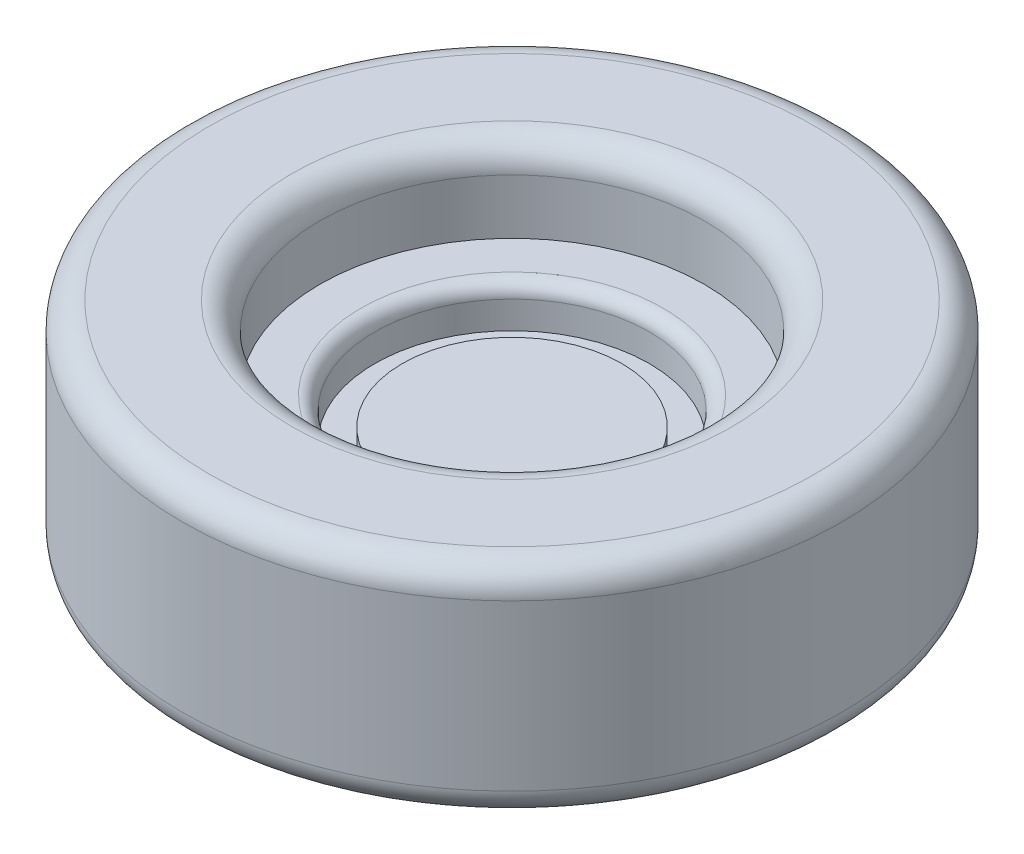
SolidWorks part; units mm, degrees
ref_plane "前视基准面" through (0, 0, 0) normal (0, 0, 1) x (1, 0, 0)
ref_plane "上视基准面" through (0, 0, 0) normal (0, 1, 0) x (1, 0, 0)
ref_plane "右视基准面" through (0, 0, 0) normal (1, 0, 0) x (0, 0, -1)
other "Configuration Table"
sketch "草图1" plane through (0, 0, 0) normal (0, 1, 0) x (1, 0, 0)
  line L1 (-20, -7.5) -> (20, -7.5)
  line L2 (-20, -7.5) -> (-20, 7.5)
  line L3 (-20, 7.5) -> (20, 7.5)
  line L4 (20, -7.5) -> (20, 7.5)
  line L5 (-20, -7.5) -> (20, 7.5) construction
  line L6 (-20, 7.5) -> (20, -7.5) construction
  point P0 (0, 0)
  dimension "D1" = 15
  dimension "D2" = 40
extrude "凸台-拉伸1" add sketch "草图1" along normal blind 1.5
sketch "草图2" plane through (0, 1.5, 0) normal (0, 1, 0) x (1, 0, 0)
  circle A0 centre (0, 0) radius 12
extrude "凸台-拉伸2" add sketch "草图2" along normal blind 8
sketch "草图3" plane through (0, 9.5, 0) normal (0, 1, 0) x (1, 0, 0)
  circle A0 centre (0, 0) radius 7
  circle A1 centre (0, 0) radius 5
extrude "切除-拉伸1" cut sketch "草图3" against normal blind 3
sketch "草图4" plane through (0, 9.5, 0) normal (0, 1, 0) x (1, 0, 0)
  circle A1 centre (0, 0) radius 5
  circle A2 centre (0, 0) radius 5
  dimension "D1" = 0
extrude "切除-拉伸2" cut sketch "草图4" against normal blind 4.5
sketch "草图5" plane through (0, 5, 0) normal (0, 1, 0) x (1, 0, 0)
  circle A0 centre (0, 0) radius 4
extrude "凸台-拉伸3" add sketch "草图5" along normal blind 0.5
fillet "圆角3" radius 1 2 edges at (0, 9.5, 7) (0, 9.5, 12)
fillet "圆角5" radius 0.5 1 edges at (0, 6.5, 5)
sketch "草图6" plane through (20, 0, 0) normal (1, 0, 0) x (0, 0, -1)
  line L4 (-7.5, 0) -> (7.5, 0)
  line L5 (7.5, 0) -> (7.5, 1.5)
  line L6 (7.5, 1.5) -> (-7.5, 1.5)
  line L7 (-7.5, 1.5) -> (-7.5, 0)
  line L8 (-7.5, 0) -> (7.5, 0)
  line L9 (7.5, 0) -> (7.5, 1.5)
  line L10 (7.5, 1.5) -> (-7.5, 1.5)
  line L11 (-7.5, 1.5) -> (-7.5, 0)
  dimension "D1" = 0
extrude "切除-拉伸3" cut sketch "草图6" against normal through all
fillet "圆角6" radius 1 1 edges at (0, 1.5, 12)
sketch "草图7" plane through (0, 1.5, 0) normal (0, -1, 0) x (1, 0, 0)
  line L1 (-2.5, 2.5) -> (2.5, 2.5)
  line L2 (-2.5, 2.5) -> (-2.5, -2.5)
  line L3 (-2.5, -2.5) -> (2.5, -2.5)
  line L4 (2.5, 2.5) -> (2.5, -2.5)
  line L5 (-2.5, 2.5) -> (2.5, -2.5) construction
  line L6 (-2.5, -2.5) -> (2.5, 2.5) construction
  point P0 (0, 0)
  dimension "D1" = 5
  dimension "D2" = 5
extrude "切除-拉伸4" cut sketch "草图7" against normal blind 1.5
